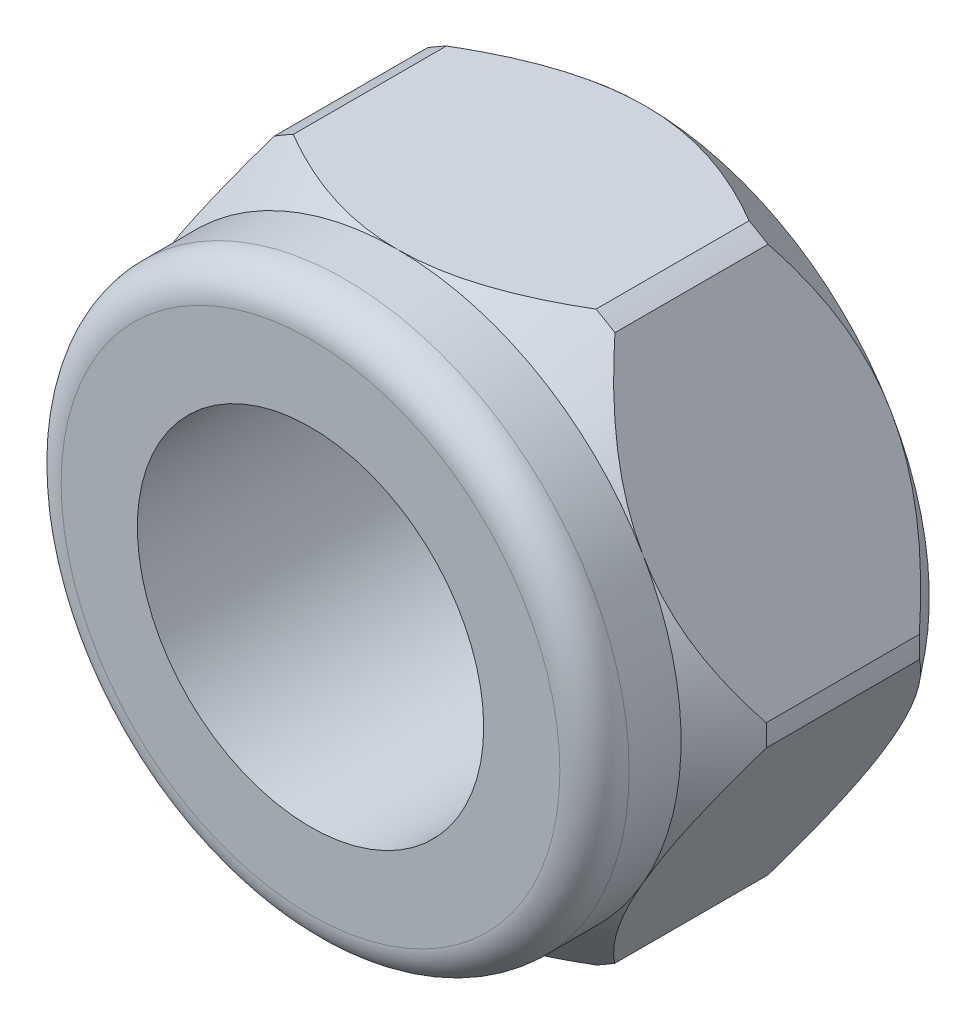
SolidWorks part; units mm, degrees
ref_plane "Front Plane" through (0, 0, 0) normal (0, 0, 1) x (1, 0, 0)
ref_plane "Top Plane" through (0, 0, 0) normal (0, 1, 0) x (1, 0, 0)
ref_plane "Right Plane" through (0, 0, 0) normal (1, 0, 0) x (0, 0, -1)
sketch "Sketch1" plane through (0, 0, 0) normal (0, 0, 1) x (1, 0, 0)
  line L0 (0, 5.6811) -> (0, 0) construction
  line L1 (0, 0) -> (5.6811, 0) construction
  line L2 (-2.8406, 4.92) -> (2.8406, 4.92)
  line L3 (2.8406, 4.92) -> (5.6811, 0)
  line L4 (2.8406, -4.92) -> (5.6811, 0)
  line L5 (-2.8406, -4.92) -> (2.8406, -4.92)
  line L6 (-2.8406, 4.92) -> (-5.6811, 0)
  line L7 (-2.8406, -4.92) -> (-5.6811, 0)
  circle A0 centre (0, 0) radius 5.6811 construction
  circle A1 centre (0, 0) radius 4.92 construction
  circle A2 centre (0, 0) radius 3
  point P12 (0, 4.92)
  point P14 (0, -4.92)
  dimension "D1" = 9.84
  dimension "D2" = 6
extrude "Boss-Extrude1" add sketch "Sketch1" along normal blind 4.3
sketch "Sketch2" plane through (0, 0, 4.3) normal (0, 0, 1) x (1, 0, 0)
  line L0 (-2.8406, 4.92) -> (-5.6811, 0) construction
  circle A0 centre (0, 0) radius 4.92
  circle A1 centre (0, 0) radius 3 construction
  circle A2 centre (0, 0) radius 3
extrude "Boss-Extrude2" add sketch "Sketch2" along normal blind 1.5
fillet "Fillet1" radius 0.6 1 edges at (4.92, 0, 5.8)
sketch "Sketch3" plane through (0, 0, 0) normal (1, 0, 0) x (0, 0, -1)
  line L0 (-4.3, 4.92) -> (-3.476, 5.575)
  line L1 (-3.476, 5.575) -> (-0.824, 5.575)
  line L2 (-0.824, 5.575) -> (0, 4.92)
  line L3 (0, 4.92) -> (0, 6.4129)
  line L4 (0, 6.4129) -> (-4.3, 6.4129)
  line L5 (-4.3, 6.4129) -> (-4.3, 4.92)
  line L8 (0, 0) -> (1.9305, 0) construction
  point P9 (-2.15, 6.4129)
  point P14 (-2.15, 5.575)
  dimension "D1" = 11.15
revolve "Cut-Revolve1" cut sketch "Sketch3" angle 360 about L8
chamfer "Chamfer1" distance 0.3 angle 45 1 edges at (3, 0, 0)
sketch "Sketch4" plane through (0, 0, 0) normal (0, 0, -1) x (-1, 0, 0)
  circle A0 centre (0, 0) radius 7.375
  dimension "D1" = 14.75
